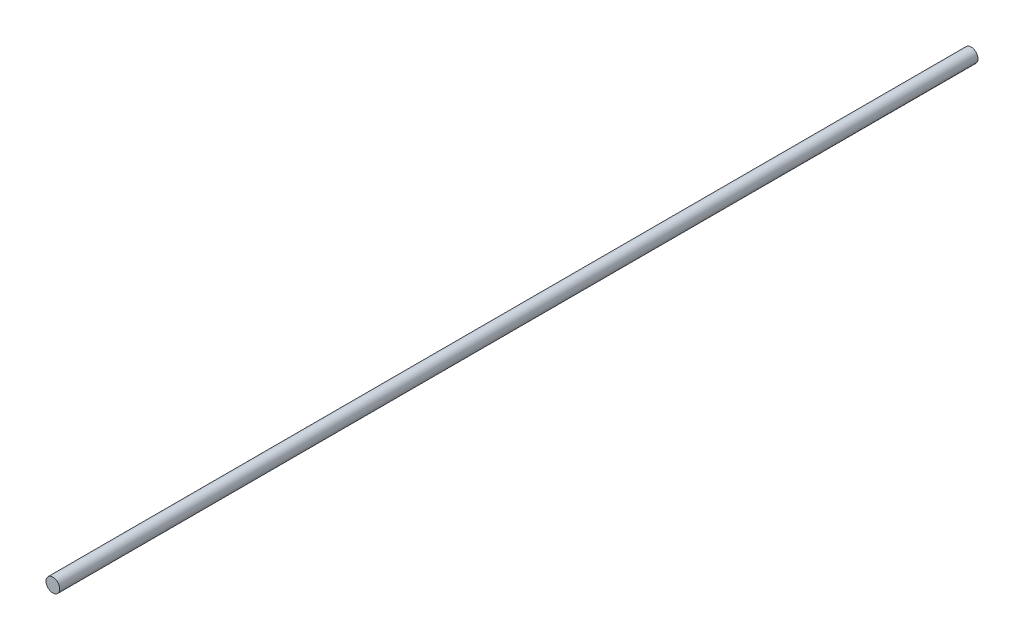
SolidWorks part; units mm, degrees
ref_plane "Front Plane" through (0, 0, 0) normal (0, 0, 1) x (1, 0, 0)
ref_plane "Top Plane" through (0, 0, 0) normal (0, 1, 0) x (1, 0, 0)
ref_plane "Right Plane" through (0, 0, 0) normal (1, 0, 0) x (0, 0, -1)
sketch "Sketch1" plane through (0, 0, 0) normal (0, 0, 1) x (1, 0, 0)
  circle A0 centre (0, 0) radius 1.5
extrude "Boss-Extrude1" add sketch "Sketch1" against normal blind 200
